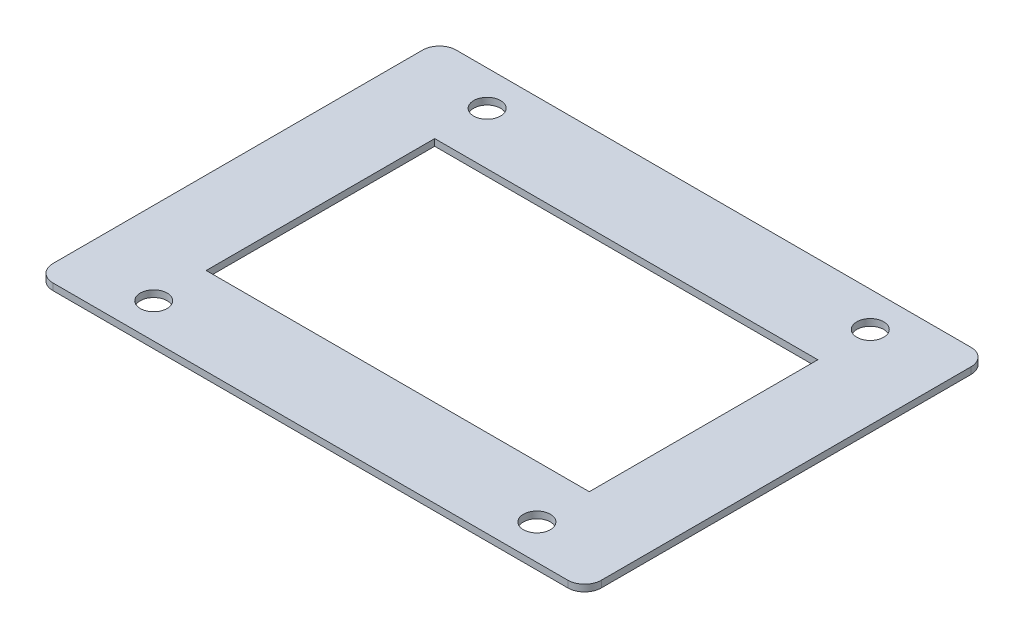
SolidWorks part; units mm, degrees
ref_plane "Alzado" through (0, 0, 0) normal (0, 0, 1) x (1, 0, 0)
ref_plane "Planta" through (0, 0, 0) normal (0, 1, 0) x (1, 0, 0)
ref_plane "Vista lateral" through (0, 0, 0) normal (1, 0, 0) x (0, 0, -1)
sketch "Croquis1" plane through (0, 0, 0) normal (0, 1, 0) x (1, 0, 0)
  line L0 (40.8, 27.5) -> (40.8, -27.5)
  line L1 (38.3, -30) -> (-38.3, -30)
  line L2 (-38.3, 30) -> (38.3, 30)
  line L3 (-40.8, -27.5) -> (-40.8, 27.5)
  circle A0 centre (28.5, -24.8) radius 2
  circle A1 centre (28.5, 24.8) radius 2
  circle A2 centre (-28.5, 24.8) radius 2
  circle A3 centre (-28.5, -24.8) radius 2
  arc A4 (38.3, -30) -> (40.8, -27.5) centre (38.3, -27.5) ccw
  arc A5 (40.8, 27.5) -> (38.3, 30) centre (38.3, 27.5) ccw
  arc A6 (-38.3, 30) -> (-40.8, 27.5) centre (-38.3, 27.5) ccw
  arc A7 (-40.8, -27.5) -> (-38.3, -30) centre (-38.3, -27.5) ccw
extrude "Saliente-Extruir2" add sketch "Croquis1" along normal blind 1
sketch "Croquis2" plane through (0, 0, 0) normal (0, 1, 0) x (1, 0, 0)
  line L1 (-28.5, 17) -> (28.5, 17)
  line L2 (-28.5, 17) -> (-28.5, -4)
  line L3 (-28.5, -17) -> (28.5, -17)
  line L4 (28.5, 17) -> (28.5, -17)
  line L5 (-28.5, 17) -> (28.5, -17) construction
  line L6 (-28.5, -17) -> (28.5, 17) construction
  line L9 (-28.5, -4) -> (-28.5, -17)
  point P0 (0, 0)
  dimension "D1" = 57
  dimension "D2" = 34
extrude "Cortar-Extruir2" cut sketch "Croquis2" along normal up to next
